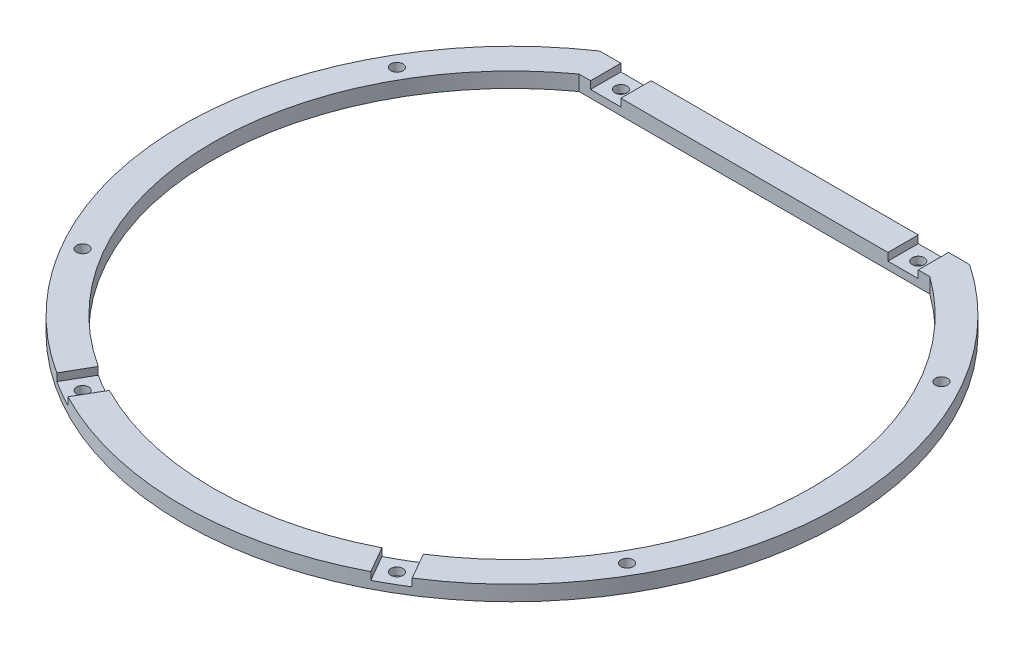
SolidWorks part; units mm, degrees
ref_plane "Front Plane" through (0, 0, 0) normal (0, 0, 1) x (1, 0, 0)
ref_plane "Top Plane" through (0, 0, 0) normal (0, 1, 0) x (1, 0, 0)
ref_plane "Right Plane" through (0, 0, 0) normal (1, 0, 0) x (0, 0, -1)
sketch "Sketch1" plane through (0, 0, 0) normal (0, 1, 0) x (1, 0, 0)
  line L0 (0, 0) -> (0, 72) construction
  line L1 (-48.8365, 72) -> (48.8365, 72)
  line L2 (-46.3141, 64) -> (46.3141, 64)
  arc A0 (-48.8365, 72) -> (48.8365, 72) centre (0, 0) ccw
  arc A1 (-46.3141, 64) -> (46.3141, 64) centre (0, 0) ccw
  dimension "D1" = 8
extrude "Boss-Extrude1" add sketch "Sketch1" along normal blind 4
sketch "Sketch2" plane through (0, 4, 0) normal (0, 1, 0) x (1, 0, 0)
  line L0 (0, 0) -> (-41.5, -71.8801) construction
  line L1 (0, 0) -> (41.5, -71.8801) construction
  line L2 (0, 0) -> (-39.2598, 68) construction
  line L3 (0, 0) -> (39.2598, 68) construction
  line L4 (-68.9797, 68) -> (70.5838, 68) construction
  line L5 (48.8365, 72) -> (-48.8365, 72) construction
  line L6 (0, 0) -> (71.8801, 41.5) construction
  line L7 (0, 0) -> (-71.8801, -41.5) construction
  line L8 (0, 0) -> (-71.8801, 41.5) construction
  line L9 (0, 0) -> (71.8801, -41.5) construction
  line L11 (-43.2598, 64) -> (-35.2598, 64)
  line L12 (-43.2598, 64) -> (-43.2598, 72)
  line L13 (-43.2598, 72) -> (-35.2598, 72)
  line L14 (-35.2598, 64) -> (-35.2598, 72)
  line L15 (-43.2598, 64) -> (-35.2598, 72) construction
  line L16 (-43.2598, 72) -> (-35.2598, 64) construction
  line L17 (35.2598, 64) -> (43.2598, 64)
  line L18 (35.2598, 64) -> (35.2598, 72)
  line L19 (35.2598, 72) -> (43.2598, 72)
  line L20 (43.2598, 64) -> (43.2598, 72)
  line L21 (35.2598, 64) -> (43.2598, 72) construction
  line L22 (35.2598, 72) -> (43.2598, 64) construction
  line L30 (-53.7582, -85.112) -> (-34.4462, -51.6626)
  line L31 (-34.4462, -51.6626) -> (-27.518, -55.6626)
  line L32 (-27.518, -55.6626) -> (-46.83, -89.112)
  line L33 (-46.83, -89.112) -> (-53.7582, -85.112)
  dimension "D1" = 4
  dimension "D4" = 4
extrude "Cut-Extrude1" cut sketch "Sketch2" against normal blind 2
mirror "Mirror1" about plane through (0, 0, 0) normal (1, 0, 0) of "Cut-Extrude1"
hole_wizard "M3 Clearance Hole1" positions "3DSketch2" profile "Sketch4" hole size "M3" standard "ANSI Metric" end condition through all
sketch3d "3DSketch2"
  point P6 (71.8801, 4, 41.5)
  point P9 (41.5, 4, 71.8801)
  point P12 (-41.5, 4, 71.8801)
  point P15 (-71.8801, 4, -41.5)
  point P23 (-71.8801, 4, 41.5)
  point P26 (71.8801, 4, -41.5)
  point P30 (-39.2598, 4, -68)
  point P33 (39.2598, 4, -68)
sketch "Sketch4" plane through (71.8801, 4, 41.5) normal (1, 0, 0) x (0, 0, 1)
  line L0 (0, 0) -> (0, 4)
  line L1 (0, 4) -> (1.6, 4)
  line L2 (1.6, 4) -> (1.6, 0)
  line L5 (1.6, 0) -> (0, 0)
  line L11 (0, -6.35) -> (0, 107.95) construction
  dimension "Thru Hole Dia." = 3.2
  dimension "Thru Hole Depth" = 4
